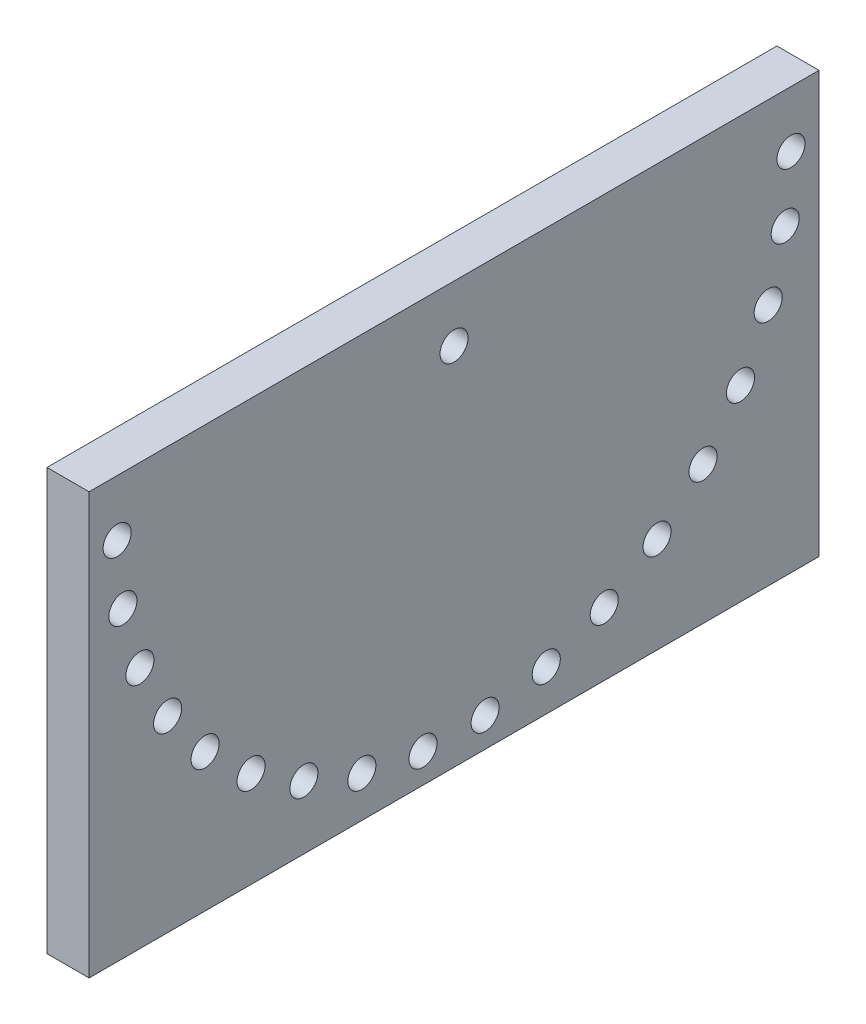
SolidWorks part; units mm, degrees
ref_plane "Front Plane" through (0, 0, 0) normal (0, 0, 1) x (1, 0, 0)
ref_plane "Top Plane" through (0, 0, 0) normal (0, 1, 0) x (1, 0, 0)
ref_plane "Right Plane" through (0, 0, 0) normal (1, 0, 0) x (0, 0, -1)
sketch "Sketch1" plane through (0, 0, 0) normal (1, 0, 0) x (0, 0, -1)
  line L1 (-130, 75) -> (130, 75)
  line L2 (-130, 75) -> (-130, -75)
  line L3 (-130, -75) -> (130, -75)
  line L4 (130, 75) -> (130, -75)
  line L5 (-130, 75) -> (130, -75) construction
  line L6 (-130, -75) -> (130, 75) construction
  point P0 (0, 0)
  dimension "D1" = 150
  dimension "D2" = 260
extrude "Boss-Extrude1" add sketch "Sketch1" along normal blind 15
sketch "Sketch3" plane through (0, 0, 0) normal (-1, 0, 0) x (0, 0, 1)
  line L0 (0, 91.3866) -> (0, -89.319) construction
  line L1 (-147.2109, 55) -> (147.2109, 55) construction
  line L2 (-130, 75) -> (130, 75) construction
  circle A0 centre (0, 55) radius 5
  dimension "D2" = 10
  dimension "D1" = 20
sketch "Sketch4" plane through (0, 0, 0) normal (-1, 0, 0) x (0, 0, 1)
  line L0 (-130, 75) -> (130, 75) construction
  line L3 (-147.2109, 55) -> (147.2109, 55) construction
  circle A0 centre (-120, 55) radius 5
  arc A1 (-120, 55) -> (120, 55) centre (0, 55) ccw construction
  circle A2 centre (-117.9568, 32.9501) radius 5
  circle A3 centre (-111.8967, 11.651) radius 5
  circle A4 centre (-102.0261, -8.1719) radius 5
  circle A5 centre (-88.6811, -25.8435) radius 5
  circle A6 centre (-72.3162, -40.7621) radius 5
  circle A7 centre (-53.4886, -52.4196) radius 5
  circle A8 centre (-32.8396, -60.4191) radius 5
  circle A9 centre (-11.0722, -64.4881) radius 5
  circle A10 centre (11.0722, -64.4881) radius 5
  circle A11 centre (32.8396, -60.4191) radius 5
  circle A12 centre (53.4886, -52.4196) radius 5
  circle A13 centre (72.3162, -40.7621) radius 5
  circle A14 centre (88.6811, -25.8435) radius 5
  circle A15 centre (102.0261, -8.1719) radius 5
  circle A16 centre (111.8967, 11.651) radius 5
  circle A17 centre (117.9568, 32.9501) radius 5
  circle A18 centre (120, 55) radius 5
  point P46 (0, 55)
  dimension "D1" = 10
  dimension "D4" = 18
  dimension "D2" = 20
  dimension "D3" = 120
extrude "Cut-Extrude1" cut sketch "Sketch3" against normal through all
extrude "Cut-Extrude2" cut sketch "Sketch4" against normal through all
